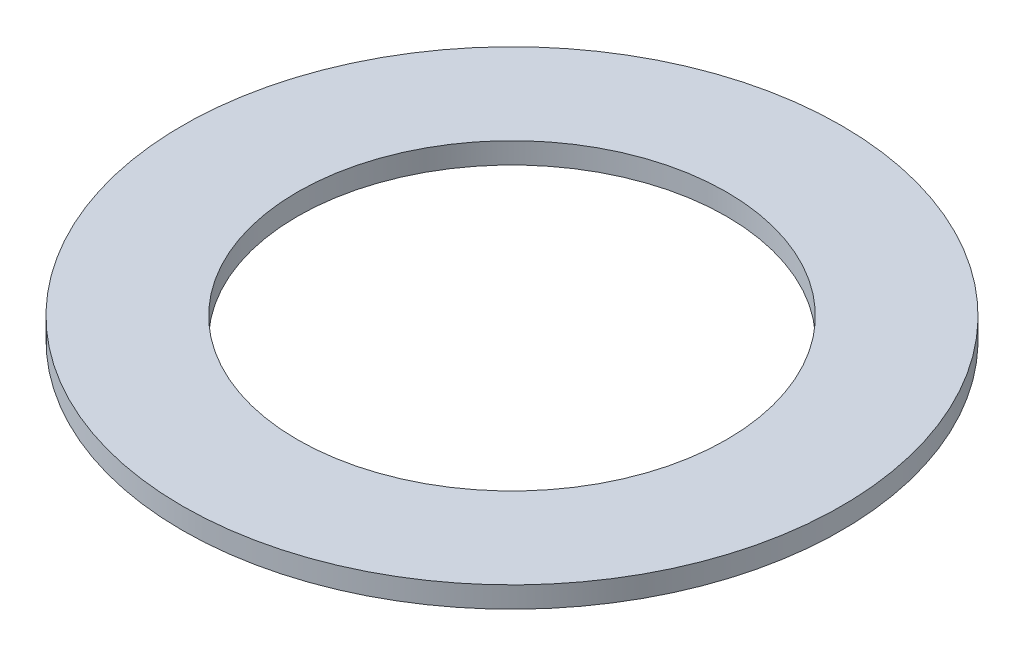
SolidWorks part; units mm, degrees
ref_plane "Front" through (0, 0, 0) normal (0, 0, 1) x (1, 0, 0)
ref_plane "Top" through (0, 0, 0) normal (0, 1, 0) x (1, 0, 0)
ref_plane "Right" through (0, 0, 0) normal (1, 0, 0) x (0, 0, -1)
ref_plane "Plane1" through (0, 0, 0) normal (0, 0, -1) x (-1, 0, 0)
sketch "Sketch1" plane through (0, 0, 0) normal (0, 0, -1) x (-1, 0, 0)
  line L0 (-8.2677, 0.8128) -> (-12.7, 0.8128)
  line L1 (-12.7, 0.8128) -> (-12.7, 0)
  line L2 (-12.7, 0) -> (-8.2677, 0)
  line L3 (-8.2677, 0) -> (-8.2677, 0.8128)
  line L4 (0, 0) -> (0, 0.8128) construction
revolve "Revolve1" add sketch "Sketch1" angle 360 about L4
